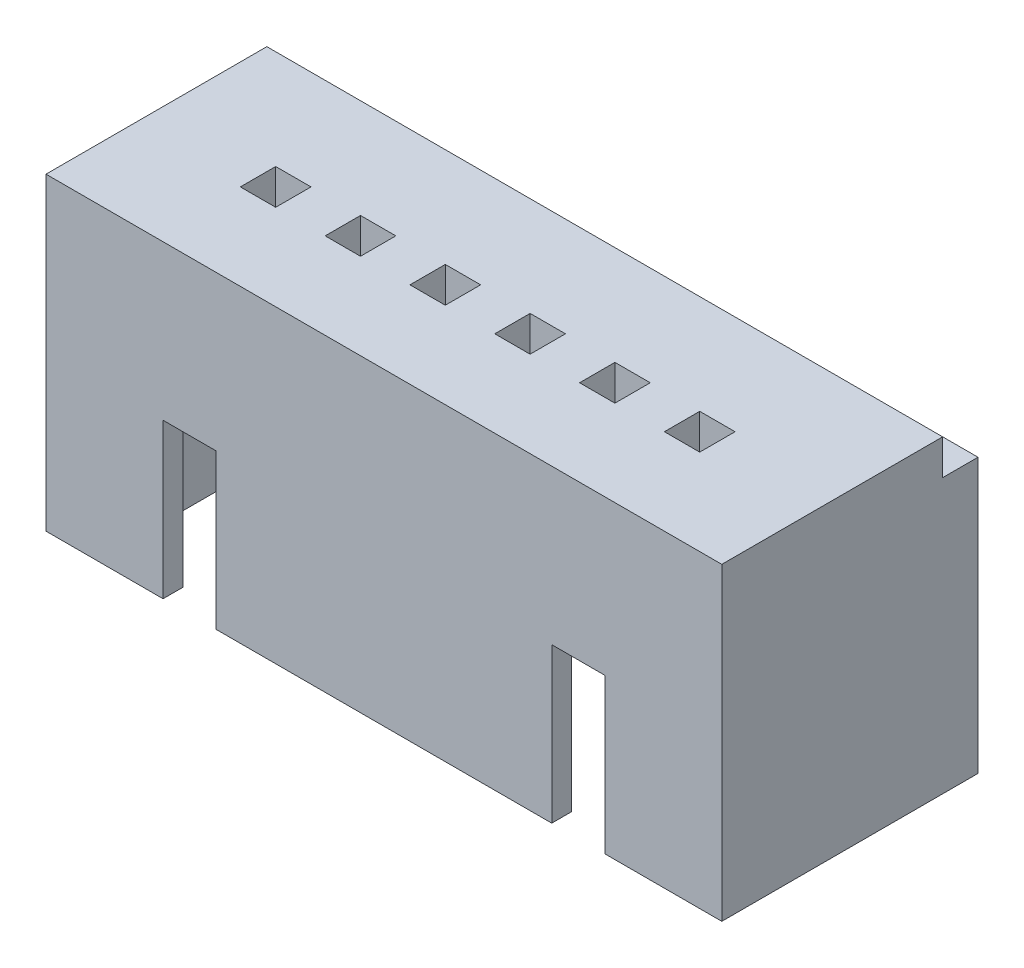
SolidWorks part; units mm, degrees
ref_plane "Front Plane" through (0, 0, 0) normal (0, 0, 1) x (1, 0, 0)
ref_plane "Top Plane" through (0, 0, 0) normal (0, 1, 0) x (1, 0, 0)
ref_plane "Right Plane" through (0, 0, 0) normal (1, 0, 0) x (0, 0, -1)
sketch "Sketch1" plane through (0, 0, 0) normal (0, 1, 0) x (1, 0, 0)
  line L1 (-7.65, -2.9) -> (7.65, -2.9)
  line L2 (-7.65, -2.9) -> (-7.65, 2.9)
  line L3 (-7.65, 2.9) -> (7.65, 2.9)
  line L4 (7.65, -2.9) -> (7.65, 2.9)
  line L5 (-7.65, -2.9) -> (7.65, 2.9) construction
  line L6 (-7.65, 2.9) -> (7.65, -2.9) construction
  point P0 (0, 0)
  dimension "D1" = 15.3
  dimension "D2" = 5.8
extrude "Boss-Extrude1" add sketch "Sketch1" along normal blind 7
sketch "Sketch3" plane through (0, 0, 0) normal (0, -1, 0) x (1, 0, 0)
  line L1 (-6.5, -2.45) -> (6.5, -2.45)
  line L2 (-6.5, -2.45) -> (-6.5, 2.45)
  line L3 (-6.5, 2.45) -> (6.5, 2.45)
  line L4 (6.5, -2.45) -> (6.5, 2.45)
  line L5 (-6.5, -2.45) -> (6.5, 2.45) construction
  line L6 (-6.5, 2.45) -> (6.5, -2.45) construction
  point P0 (0, 0)
  dimension "D1" = 13
  dimension "D2" = 4.9
extrude "Cut-Extrude1" cut sketch "Sketch3" against normal blind 5
sketch "Sketch4" plane through (0, 0, 2.9) normal (0, 0, 1) x (1, 0, 0)
  line L0 (-7.65, 0) -> (7.65, 0) construction
  line L1 (-5, 0) -> (-3.8, 0)
  line L2 (-5, 0) -> (-5, 3.5)
  line L3 (-5, 3.5) -> (-3.8, 3.5)
  line L4 (-3.8, 0) -> (-3.8, 3.5)
  line L6 (3.8, 0) -> (5, 0)
  line L7 (3.8, 0) -> (3.8, 3.5)
  line L8 (3.8, 3.5) -> (5, 3.5)
  line L9 (5, 0) -> (5, 3.5)
  dimension "D1" = 1.2
  dimension "D2" = 1.2
  dimension "D3" = 5
  dimension "D4" = 10
  dimension "D5" = 3.5
extrude "Cut-Extrude2" cut sketch "Sketch4" against normal blind 4
sketch "Sketch5" plane through (0, 7, 0) normal (0, 1, 0) x (1, 0, 0)
  line L0 (7.65, -2.9) -> (7.65, 2.9) construction
  line L1 (7.65, 2.1) -> (-7.65, 2.1)
  line L2 (7.65, 2.1) -> (7.65, 2.9)
  line L3 (7.65, 2.9) -> (-7.65, 2.9)
  line L4 (-7.65, 2.1) -> (-7.65, 2.9)
  dimension "D1" = 0.8
extrude "Cut-Extrude3" cut sketch "Sketch5" against normal blind 0.8 contours L1 L4 L3 L2
sketch "Sketch6" plane through (0, 7, 0) normal (0, 1, 0) x (1, 0, 0)
  line L0 (2.48, -0.15) -> (2.48, -0.95) construction
  line L2 (5.2, -0.95) -> (4.4, -0.95)
  line L3 (5.2, -0.95) -> (5.2, -0.15)
  line L4 (5.2, -0.15) -> (4.4, -0.15)
  line L5 (4.4, -0.95) -> (4.4, -0.15)
  line L6 (3.28, -0.95) -> (2.48, -0.95)
  line L7 (3.28, -0.95) -> (3.28, -0.15)
  line L8 (3.28, -0.15) -> (2.48, -0.15)
  line L9 (2.48, -0.95) -> (2.48, -0.15)
  line L11 (1.36, -0.95) -> (0.56, -0.95)
  line L12 (1.36, -0.95) -> (1.36, -0.15)
  line L13 (1.36, -0.15) -> (0.56, -0.15)
  line L14 (0.56, -0.95) -> (0.56, -0.15)
  line L15 (-0.56, -0.95) -> (-1.36, -0.95)
  line L16 (-0.56, -0.95) -> (-0.56, -0.15)
  line L17 (-0.56, -0.15) -> (-1.36, -0.15)
  line L18 (-1.36, -0.95) -> (-1.36, -0.15)
  line L19 (-2.48, -0.95) -> (-3.28, -0.95)
  line L20 (-2.48, -0.95) -> (-2.48, -0.15)
  line L21 (-2.48, -0.15) -> (-3.28, -0.15)
  line L22 (-3.28, -0.95) -> (-3.28, -0.15)
  line L23 (-4.4, -0.95) -> (-5.2, -0.95)
  line L24 (-4.4, -0.95) -> (-4.4, -0.15)
  line L25 (-4.4, -0.15) -> (-5.2, -0.15)
  line L26 (-5.2, -0.95) -> (-5.2, -0.15)
extrude "Cut-Extrude4" cut sketch "Sketch6" against normal blind 10
sketch "Sketch7" plane through (0, 5, 0) normal (0, -1, 0) x (1, 0, 0)
  line L0 (6.5, -2.45) -> (6.5, 2.45) construction
  line L1 (-6.5, -2.45) -> (6.5, -2.45)
  line L2 (-6.5, -2.45) -> (-6.5, -1.45)
  line L3 (-6.5, -1.45) -> (6.5, -1.45)
  line L4 (6.5, -2.45) -> (6.5, -1.45)
  dimension "D1" = 1
extrude "Cut-Extrude5" cut sketch "Sketch7" against normal blind 0.3
